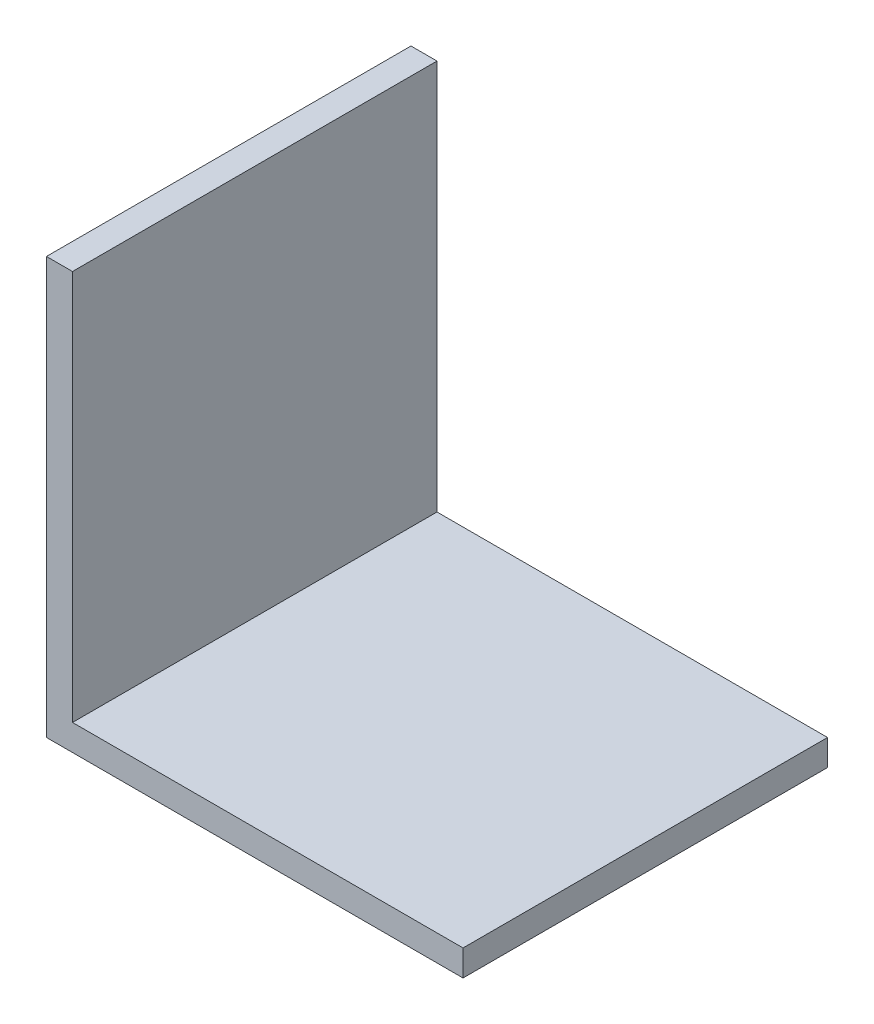
SolidWorks part; units mm, degrees
ref_plane "Front Plane" through (0, 0, 0) normal (0, 0, 1) x (1, 0, 0)
ref_plane "Top Plane" through (0, 0, 0) normal (0, 1, 0) x (1, 0, 0)
ref_plane "Right Plane" through (0, 0, 0) normal (1, 0, 0) x (0, 0, -1)
sketch "Sketch2" plane through (0, 0, 0) normal (0, 0, 1) x (1, 0, 0)
  line L0 (0, 0) -> (0, 76.2)
  line L1 (0, 76.2) -> (4.7625, 76.2)
  line L2 (4.7625, 76.2) -> (4.7625, 4.7625)
  line L3 (4.7625, 4.7625) -> (76.2, 4.7625)
  line L4 (76.2, 4.7625) -> (76.2, 0)
  line L5 (76.2, 0) -> (0, 0)
  dimension "D1" = 76.2
  dimension "D2" = 4.7625
extrude "Boss-Extrude1" add sketch "Sketch2" along normal mid plane 66.675
